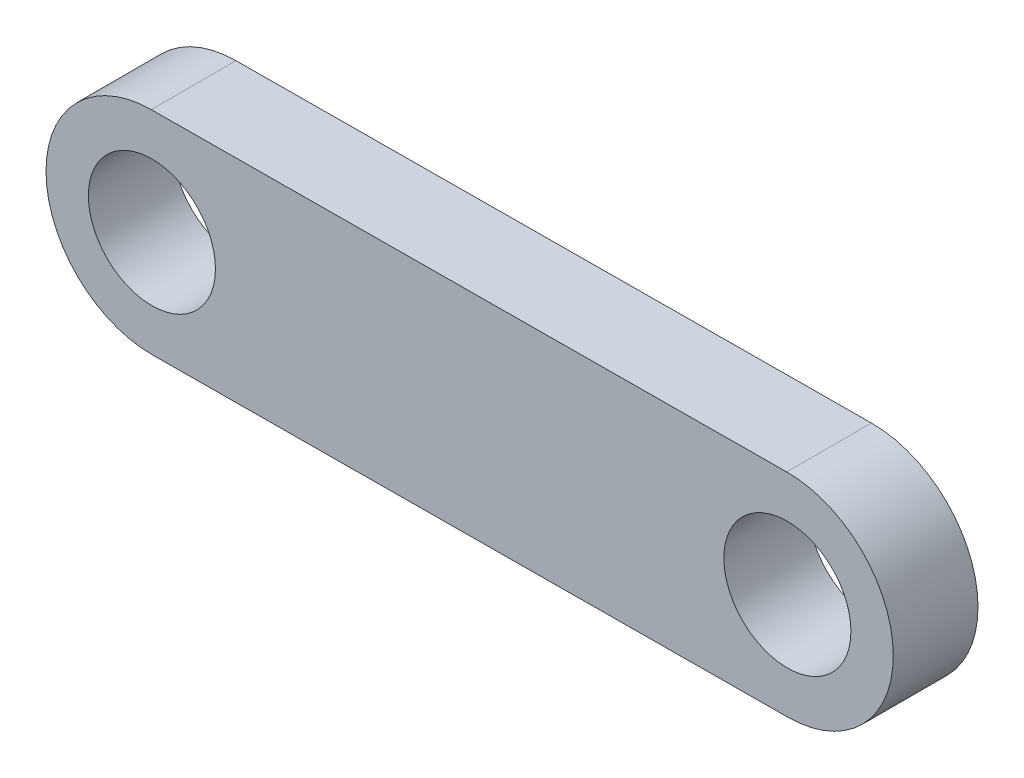
SolidWorks part; units mm, degrees
ref_plane "Front Plane" through (0, 0, 0) normal (0, 0, 1) x (1, 0, 0)
ref_plane "Top Plane" through (0, 0, 0) normal (0, 1, 0) x (1, 0, 0)
ref_plane "Right Plane" through (0, 0, 0) normal (1, 0, 0) x (0, 0, -1)
sketch "Sketch1" plane through (0, 0, 0) normal (0, 0, 1) x (1, 0, 0)
  line L0 (0, 0) -> (15, 0.0936) construction
  line L1 (-0.0156, 2.5) -> (14.9844, 2.5936)
  line L2 (0.0156, -2.5) -> (15.0156, -2.4063)
  arc A0 (-0.0156, 2.5) -> (0.0156, -2.5) centre (0, 0) ccw
  arc A1 (15.0156, -2.4063) -> (14.9844, 2.5936) centre (15, 0.0936) ccw
  circle A2 centre (0, 0) radius 1.5
  circle A3 centre (15, 0.0936) radius 1.5
  point P3 (7.5, 0.0468)
  dimension "D3" = 3
  dimension "D4" = 3
  dimension "D1" = 15
  dimension "D2" = 5
extrude "Boss-Extrude2" add sketch "Sketch1" along normal blind 2
